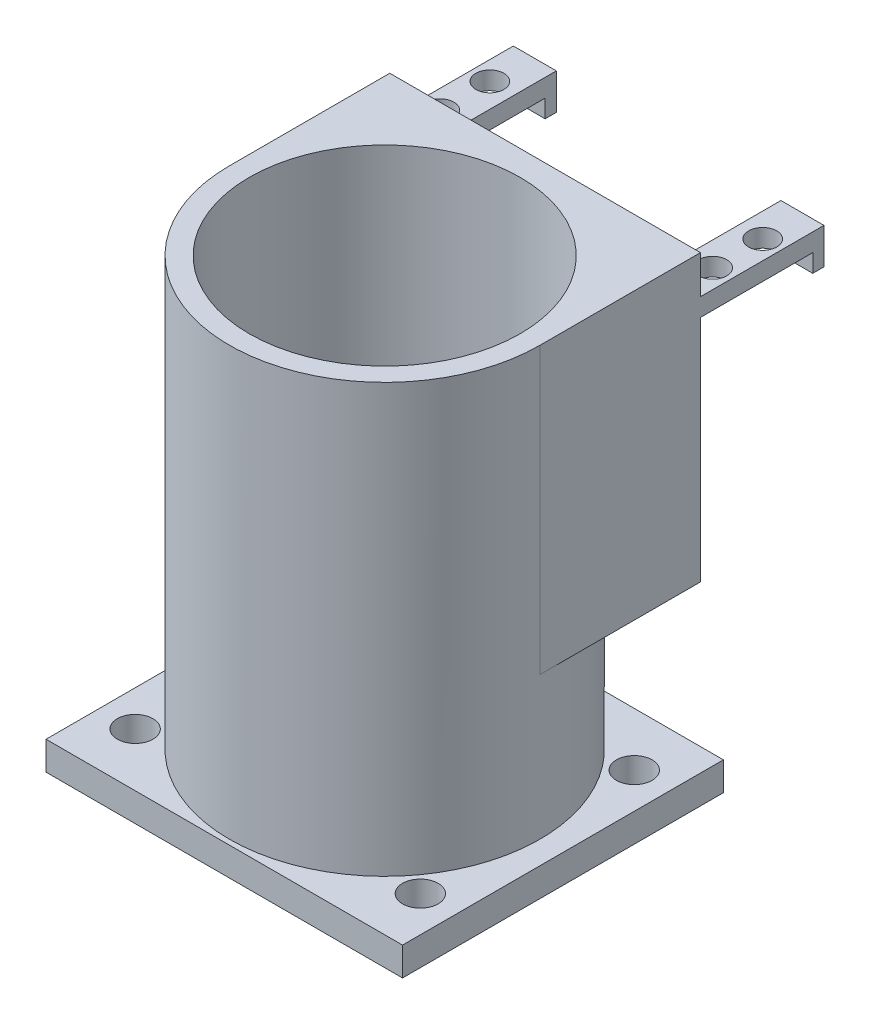
SolidWorks part; units mm, degrees
ref_plane "Front Plane" through (0, 0, 0) normal (0, 0, 1) x (1, 0, 0)
ref_plane "Top Plane" through (0, 0, 0) normal (0, 1, 0) x (1, 0, 0)
ref_plane "Right Plane" through (0, 0, 0) normal (1, 0, 0) x (0, 0, -1)
sketch "Sketch1" plane through (0, 0, 0) normal (0, 1, 0) x (1, 0, 0)
  line L0 (0, -9.525) -> (6.35, -9.525) construction
  line L1 (0, 0) -> (63.5, 0)
  line L2 (0, 0) -> (0, -57.15)
  line L3 (0, -57.15) -> (63.5, -57.15)
  line L4 (63.5, 0) -> (63.5, -57.15)
  line L5 (57.15, -9.525) -> (63.5, -9.525) construction
  line L6 (0, -28.575) -> (63.5, -28.575) construction
  circle A0 centre (6.35, -9.525) radius 3.175
  circle A1 centre (57.15, -9.525) radius 3.175
  circle A4 centre (57.15, -47.625) radius 3.175
  circle A5 centre (6.35, -47.625) radius 3.175
  dimension "D3" = 50.8
  dimension "D4" = 6.35
  dimension "D1" = 63.5
  dimension "D2" = 57.15
  dimension "D5" = 9.525
extrude "Boss-Extrude1" add sketch "Sketch1" along normal blind 5.08
sketch "Sketch2" plane through (0, 5.08, 0) normal (0, 1, 0) x (1, 0, 0)
  line L0 (31.75, 0) -> (31.75, -57.15) construction
  line L1 (63.5, 0) -> (0, 0) construction
  line L2 (0, -57.15) -> (63.5, -57.15) construction
  line L3 (0, -28.575) -> (63.5, -28.575) construction
  line L4 (0, 0) -> (0, -57.15) construction
  line L5 (63.5, -57.15) -> (63.5, 0) construction
  circle A0 centre (31.75, -28.575) radius 24.13
  circle A1 centre (31.75, -28.575) radius 27.67
  dimension "D1" = 55.34
extrude "Boss-Extrude2" add sketch "Sketch2" along normal blind 76.2 contours A1 | A0
sketch "Sketch4" plane through (0, 0, 0) normal (0, 0, -1) x (-1, 0, 0)
  line L7 (-31.75, 81.28) -> (-31.75, 0) construction
  line L8 (-4.08, 81.28) -> (-59.42, 81.28) construction
  line L9 (-63.5, 0) -> (0, 0) construction
  line L11 (-59.42, 81.28) -> (-4.08, 81.28)
  line L12 (-59.42, 81.28) -> (-59.42, 30.48)
  line L13 (-59.42, 30.48) -> (-4.08, 30.48)
  line L14 (-4.08, 81.28) -> (-4.08, 30.48)
  dimension "D1" = 55.34
  dimension "D2" = 50.8
extrude "Boss-Extrude3" add sketch "Sketch4" against normal up to surface (28.575 mm away)
sketch "Sketch5" plane through (0, 0, 0) normal (0, 0, -1) x (-1, 0, 0)
  line L0 (-4.08, 30.48) -> (-4.08, 81.28) construction
  line L3 (-59.42, 74.48) -> (-4.08, 74.48) construction
  line L5 (-31.75, 81.28) -> (-31.75, 5.08) construction
  line L6 (-4.08, 81.28) -> (-59.42, 81.28) construction
  line L7 (-63.5, 5.08) -> (0, 5.08) construction
  line L16 (-59.42, 81.28) -> (-59.42, 30.48) construction
  line L17 (-11.75, 71.28) -> (-4.08, 71.28)
  line L18 (-51.75, 74.48) -> (-59.42, 74.48)
  line L19 (-51.75, 74.48) -> (-51.75, 71.28)
  line L20 (-51.75, 71.28) -> (-59.42, 71.28)
  line L21 (-59.42, 74.48) -> (-59.42, 71.28)
  line L22 (-4.08, 74.48) -> (-4.08, 71.28)
  line L23 (-11.75, 74.48) -> (-4.08, 74.48)
  line L24 (-11.75, 74.48) -> (-11.75, 71.28)
  line L25 (-4.08, 30.48) -> (-4.08, 81.28) construction
  dimension "D1" = 6.8
  dimension "D2" = 20
  dimension "D3" = 3.2
extrude "Boss-Extrude4" add sketch "Sketch5" along normal blind 20
sketch "Sketch6" plane through (0, 71.28, 0) normal (0, -1, 0) x (1, 0, 0)
  line L0 (4.08, -10) -> (59.42, -10) construction
  line L1 (4.08, -20) -> (4.08, 0) construction
  line L2 (59.42, -20) -> (59.42, 0) construction
  line L3 (11.75, -20) -> (11.75, 0) construction
  line L4 (31.75, 0) -> (31.75, -20) construction
  line L5 (63.5, 0) -> (0, 0) construction
  circle A0 centre (7.45, -5.55) radius 2.5
  circle A1 centre (56.05, -5.55) radius 2.5
  circle A3 centre (56.05, -14.45) radius 2.5
  circle A4 centre (7.45, -14.45) radius 2.5
  dimension "D3" = 5
  dimension "D1" = 4.3
  dimension "D2" = 4.45
extrude "Cut-Extrude1" cut sketch "Sketch6" against normal through all
sketch "Sketch7" plane through (0, 0, -20) normal (0, 0, -1) x (-1, 0, 0)
  line L1 (-59.42, 74.48) -> (-51.75, 74.48)
  line L2 (-59.42, 74.48) -> (-59.42, 71.28)
  line L3 (-59.42, 71.28) -> (-51.75, 71.28)
  line L4 (-51.75, 74.48) -> (-51.75, 71.28)
  line L5 (-11.75, 74.48) -> (-4.08, 74.48)
  line L6 (-11.75, 74.48) -> (-11.75, 71.28)
  line L7 (-11.75, 71.28) -> (-4.08, 71.28)
  line L8 (-4.08, 74.48) -> (-4.08, 71.28)
extrude "Boss-Extrude5" add sketch "Sketch7" along normal blind 2
sketch "Sketch8" plane through (0, 71.28, 0) normal (0, -1, 0) x (1, 0, 0)
  line L0 (4.08, -22) -> (4.08, 0) construction
  line L1 (4.08, -20) -> (11.75, -20)
  line L2 (4.08, -20) -> (4.08, -22)
  line L3 (4.08, -22) -> (11.75, -22)
  line L4 (11.75, -20) -> (11.75, -22)
  line L5 (31.75, 0) -> (31.75, -22) construction
  line L6 (63.5, 0) -> (0, 0) construction
  line L7 (59.42, -22) -> (51.75, -22)
  line L8 (51.75, -20) -> (51.75, -22)
  line L9 (59.42, -20) -> (51.75, -20)
  line L10 (59.42, -20) -> (59.42, -22)
  dimension "D1" = 2
extrude "Boss-Extrude6" add sketch "Sketch8" along normal blind 3.2
